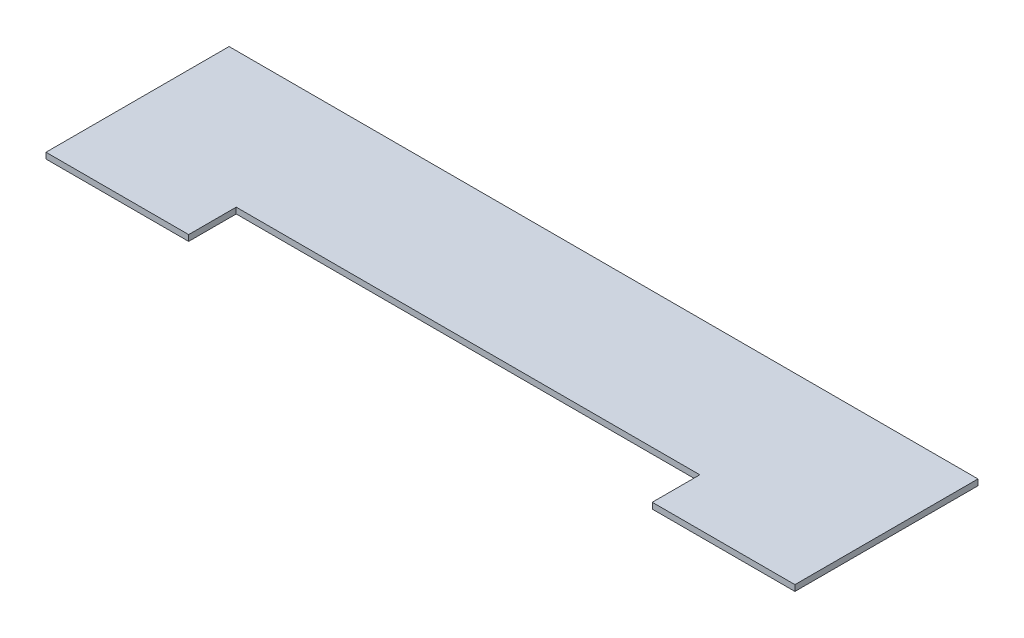
SolidWorks part; units mm, degrees
ref_plane "Front Plane" through (0, 0, 0) normal (0, 0, 1) x (1, 0, 0)
ref_plane "Top Plane" through (0, 0, 0) normal (0, 1, 0) x (1, 0, 0)
ref_plane "Right Plane" through (0, 0, 0) normal (1, 0, 0) x (0, 0, -1)
sketch "Sketch1" plane through (0, 0, 0) normal (0, 1, 0) x (1, 0, 0)
  line L1 (0, 0) -> (800.1, 0)
  line L2 (0, 0) -> (0, 195.58)
  line L3 (0, 195.58) -> (800.1, 195.58)
  line L4 (800.1, 0) -> (800.1, 195.58)
  dimension "D1" = 800.1
  dimension "D2" = 195.58
extrude "Boss-Extrude2" add sketch "Sketch1" along normal blind 6.35 contours L1 L4 L3 L2
sketch "Sketch3" plane through (0, 6.35, 0) normal (0, 1, 0) x (1, 0, 0)
  line L0 (0, 0) -> (800.1, 0) construction
  line L1 (152.4, 50.8) -> (647.7, 50.8)
  line L2 (152.4, 50.8) -> (152.4, 0)
  line L3 (152.4, 0) -> (647.7, 0)
  line L4 (647.7, 50.8) -> (647.7, 0)
  line L5 (0, 0) -> (0, 195.58) construction
  line L6 (800.1, 0) -> (800.1, 195.58) construction
  dimension "D1" = 50.8
  dimension "D2" = 152.4
  dimension "D3" = 152.4
extrude "Cut-Extrude1" cut sketch "Sketch3" against normal blind 6.35 contours L1 L4 L3 L2
sketch "Sketch4" plane through (0, 6.35, 0) normal (0, 1, 0) x (1, 0, 0)
  line L0 (152.4, 50.8) -> (647.7, 50.8) construction
  line L2 (152.4, 50.8) -> (152.4, 0) construction
  circle A0 centre (203.2, 63.5) radius 3.175
  dimension "D1" = 6.35
  dimension "D2" = 12.7
  dimension "D3" = 50.8
